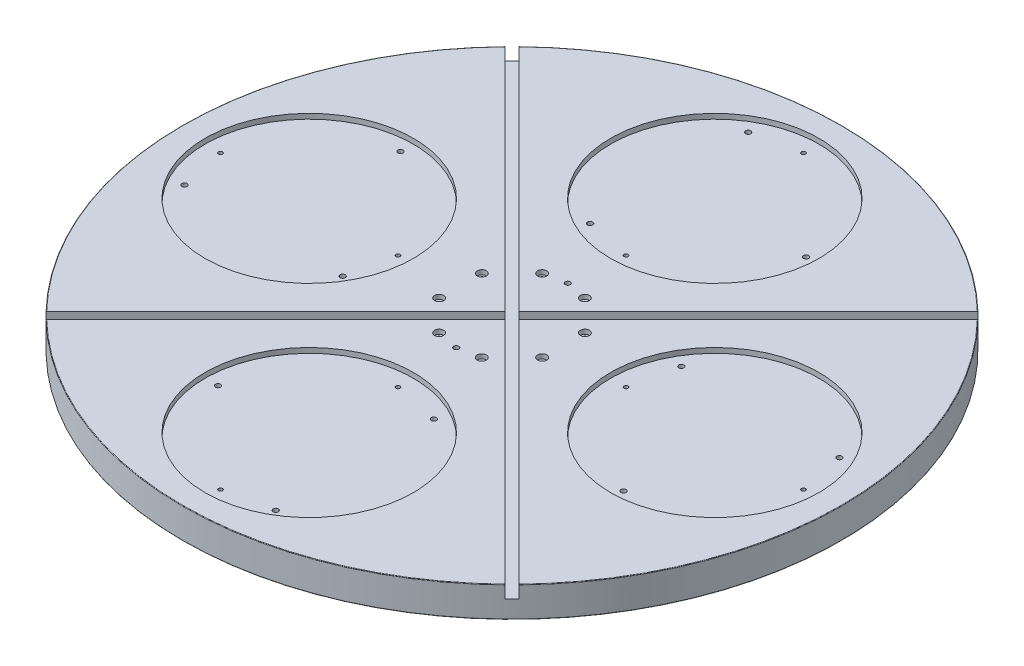
SolidWorks part; units mm, degrees
material "3003 Alloy"
ref_plane "Front Plane" through (0, 0, 0) normal (0, 0, 1) x (1, 0, 0)
ref_plane "Top Plane" through (0, 0, 0) normal (0, 1, 0) x (1, 0, 0)
ref_plane "Right Plane" through (0, 0, 0) normal (1, 0, 0) x (0, 0, -1)
sketch "Sketch1" plane through (0, 0, 0) normal (0, 1, 0) x (1, 0, 0)
  circle A0 centre (0, 0) radius 650
  dimension "1400" = 1300
extrude "Boss-Extrude1" add sketch "Sketch1" against normal blind 60
sketch "Sketch2" plane through (0, 0, 0) normal (0, 1, 0) x (1, 0, 0)
  circle A0 centre (0, 0) radius 400
  circle A1 centre (0, 400) radius 205.5
  circle A2 centre (400, 0) radius 205.5
  circle A3 centre (0, -400) radius 205.5
  circle A4 centre (-400, 0) radius 205.5
  point P14 (0, 0)
  dimension "D1" = 4
  dimension "410" = 411
  dimension "700" = 800
extrude "Cut-Extrude1" cut sketch "Sketch2" against normal blind 10 contours A1 | A4 | A2 | A3
sketch "Sketch3" plane through (0, -10, 0) normal (0, 1, 0) x (1, 0, 0)
  circle A0 centre (0, 575) radius 4
  circle A1 centre (0, 225) radius 4
  circle A2 centre (0, 400) radius 205.5 construction
  dimension "D1" = 8
  dimension "D2" = 8
  dimension "D3" = 350
  dimension "D4" = 175
extrude "Cut-Extrude2" cut sketch "Sketch3" against normal blind 25
sketch "Sketch4" plane through (0, -10, 0) normal (0, 1, 0) x (1, 0, 0)
  line L0 (-205.5, 400) -> (205.5, 400) construction
  circle A1 centre (0, 400) radius 205.5 construction
  circle A2 centre (0, 400) radius 205.5 construction
  point P0 (180, 400)
  point P9 (0, 400)
  point P16 (-90, 244.1154)
  point P17 (-90, 555.8846)
  point P18 (0, 400)
  dimension "D2" = 3
  dimension "D1" = 180
hole_wizard "M12 Tapped Hole1" positions "Sketch8" profile "Sketch9" tap size "M12" standard "ISO"
sketch "Sketch8" plane through (0, -10, 0) normal (0, 1, 0) x (1, 0, 0)
  point P0 (180, 400)
  point P3 (-90, 555.8846)
  point P6 (-90, 244.1154)
sketch "Sketch9" plane through (180, -10, -400) normal (1, 0, 0) x (0, 0, 1)
  line L0 (0, 0) -> (0, 29.25)
  line L1 (0, 29.25) -> (5.1, 26.1856)
  line L2 (5.1, 26.1856) -> (5.1, 0)
  line L5 (5.1, 0) -> (0, 0)
  line L10 (0, 29.25) -> (-5.1, 26.1856) construction
  line L11 (0, -6.35) -> (0, 107.95) construction
  dimension "Tap Drill Dia." = 10.2
  dimension "Tap Drill Depth" = 29.25
  dimension "Drill Angle" = 118
cosmetic thread "Hole Thread1" parameters "D1"=24, "D2"=12
cosmetic thread "Hole Thread2" parameters "D1"=24, "D2"=12
cosmetic thread "Hole Thread3" parameters "D1"=24, "D2"=12
pattern_circular "CirPattern1" count 4 over 360 about axis through (0, 0, 0) along (0, 1, 0) of "M12 Tapped Hole1", "Cut-Extrude2"
cosmetic thread "Hole Thread4" parameters "D1"=24, "D2"=12
cosmetic thread "Hole Thread5" parameters "D1"=24, "D2"=12
cosmetic thread "Hole Thread6" parameters "D1"=24, "D2"=12
cosmetic thread "Hole Thread7" parameters "D1"=24, "D2"=12
cosmetic thread "Hole Thread8" parameters "D1"=24, "D2"=12
cosmetic thread "Hole Thread9" parameters "D1"=24, "D2"=12
cosmetic thread "Hole Thread10" parameters "D1"=24, "D2"=12
cosmetic thread "Hole Thread11" parameters "D1"=24, "D2"=12
cosmetic thread "Hole Thread12" parameters "D1"=24, "D2"=12
fillet "Fillet1" radius 1 2 edges at (0, -60, 650) (0, 0, 650)
sketch "Sketch10" plane through (0, 0, 0) normal (0, 1, 0) x (1, 0, 0)
  circle A0 centre (0, 110) radius 5
  circle A1 centre (0, -110) radius 5
  dimension "D1" = 10
  dimension "D2" = 110
  dimension "D3" = 110
extrude "Cut-Extrude4" cut sketch "Sketch10" against normal through all
sketch "Sketch11" plane through (0, 0, 0) normal (0, 1, 0) x (1, 0, 0)
  line L0 (0, 0) -> (-110, 0) construction
  line L1 (0, 0) -> (-101.6267, 42.0952) construction
  circle A0 centre (0, 0) radius 110
  circle A1 centre (-101.6267, 42.0952) radius 4.5
  circle A9 centre (-42.0952, 101.6267) radius 4.5
  circle A10 centre (42.0952, 101.6267) radius 4.5
  circle A11 centre (101.6267, 42.0952) radius 4.5
  circle A12 centre (101.6267, -42.0952) radius 4.5
  circle A13 centre (42.0952, -101.6267) radius 4.5
  circle A14 centre (-42.0952, -101.6267) radius 4.5
  circle A15 centre (-101.6267, -42.0952) radius 4.5
  point P23 (0, -35.9305)
  point P24 (0, 0)
  dimension "D2" = 9
  dimension "D1" = 22.5
  dimension "D3" = 8
extrude "Cut-Extrude5" cut sketch "Sketch11" against normal through all
sketch "Sketch12" plane through (0, 0, 0) normal (0, 1, 0) x (1, 0, 0)
  circle A0 centre (-42.0952, 101.6267) radius 9
  circle A1 centre (42.0952, 101.6267) radius 9
  circle A2 centre (101.6267, 42.0952) radius 9
  circle A3 centre (101.6267, -42.0952) radius 9
  circle A4 centre (42.0952, -101.6267) radius 9
  circle A5 centre (-42.0952, -101.6267) radius 9
  circle A6 centre (-101.6267, -42.0952) radius 9
  circle A7 centre (-101.6267, 42.0952) radius 9
  dimension "D1" = 18
extrude "Cut-Extrude6" cut sketch "Sketch12" against normal blind 8.8
sketch "Sketch14" plane through (0, -60, 0) normal (0, -1, 0) x (1, 0, 0)
  circle A0 centre (0, 0) radius 90
  dimension "D1" = 180
extrude "Cut-Extrude8" cut sketch "Sketch14" against normal blind 7
sketch "Sketch15" plane through (0, 0, 0) normal (0, 1, 0) x (1, 0, 0)
  line L0 (0, 0) -> (0, 649) construction
  line L1 (0, 0) -> (463.5221, 463.5221) construction
  line L2 (469.1675, -469.1675) -> (0, 0) construction
  line L3 (0, 0) -> (-480.6419, -480.6419) construction
  line L4 (0, 0) -> (-468.2029, 468.2029) construction
  line L5 (7.0711, 7.0711) -> (-461.1319, 475.274)
  line L6 (-7.0711, 7.0711) -> (-487.713, -473.5708)
  line L7 (476.2386, -462.0964) -> (7.0711, 7.0711)
  line L8 (7.0711, -7.0711) -> (470.5932, 456.451)
  line L9 (-7.0711, -7.0711) -> (-475.274, 461.1319)
  line L10 (7.0711, -7.0711) -> (-473.5708, -487.713)
  line L11 (462.0964, -476.2386) -> (-7.0711, -7.0711)
  line L12 (-7.0711, 7.0711) -> (456.451, 470.5932)
  line L13 (7.0711, 7.0711) -> (-7.0711, -7.0711)
  line L14 (-461.1319, 475.274) -> (-475.274, 461.1319)
  line L15 (-7.0711, 7.0711) -> (7.0711, -7.0711)
  line L16 (-487.713, -473.5708) -> (-473.5708, -487.713)
  line L17 (476.2386, -462.0964) -> (462.0964, -476.2386)
  line L18 (7.0711, 7.0711) -> (-7.0711, -7.0711)
  line L19 (7.0711, -7.0711) -> (-7.0711, 7.0711)
  line L20 (470.5932, 456.451) -> (456.451, 470.5932)
  circle A0 centre (0, 0) radius 649 construction
  point P8 (-438.6676, 478.3009)
  point P11 (-446.8579, 488.6164)
  point P12 (0, 0)
  point P13 (444.5373, 481.7593)
  point P14 (0, 0)
  point P15 (429.8684, -505.4201)
  point P16 (0, 0)
  point P17 (-479.1353, -482.1438)
  circle M16 centre (0, 0) radius 649
  dimension "D1" = 45
  dimension "D2" = 90
  dimension "D3" = 90
  dimension "D4" = 90
  dimension "D5" = 10
  dimension "D6" = 10
extrude "Cut-Extrude9" cut sketch "Sketch15" against normal blind 25 contours L10 L11 L9 L6 M16 | L11 L7 L8 L10 M16 | L12 L5 L7 L8 M16 | L6 L12 L5 L9 M16 | L15 L6 L9 L13 | L15 L13 L11 L10 | L13 L15 L8 L7 | L12 L15 L13 L5 | L6 L16 L10 M16 | L5 L14 L9 M16 | L8 L20 L12 M16 | L17 L7 L11 M16
